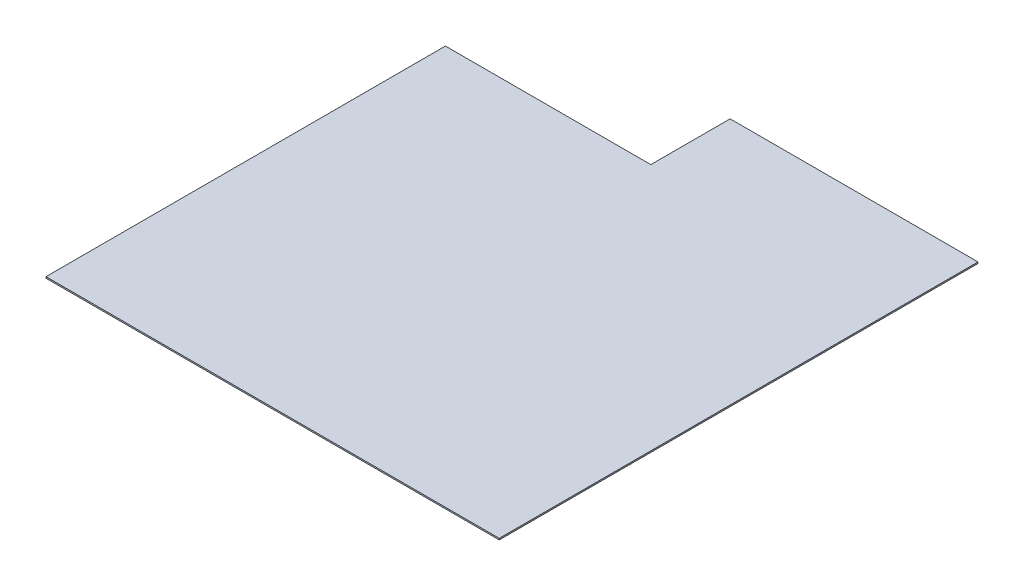
SolidWorks part; units mm, degrees
material "Pine"
ref_plane "Front Plane" through (0, 0, 0) normal (0, 0, 1) x (1, 0, 0)
ref_plane "Top Plane" through (0, 0, 0) normal (0, 1, 0) x (1, 0, 0)
ref_plane "Right Plane" through (0, 0, 0) normal (1, 0, 0) x (0, 0, -1)
sketch "Sketch1" plane through (0, 0, 0) normal (0, 1, 0) x (1, 0, 0)
  line L0 (0, 0) -> (0, 1073.15)
  line L1 (0, 1073.15) -> (-555.625, 1073.15)
  line L2 (-555.625, 1073.15) -> (-555.625, 895.35)
  line L3 (-555.625, 895.35) -> (-1016, 895.35)
  line L4 (-1016, 895.35) -> (-1016, 0)
  line L5 (-1016, 0) -> (0, 0)
  dimension "D1" = 1016
  dimension "D2" = 1073.15
  dimension "D3" = 177.8
  dimension "D4" = 460.375
extrude "Boss-Extrude1" add sketch "Sketch1" along normal blind 3.175
